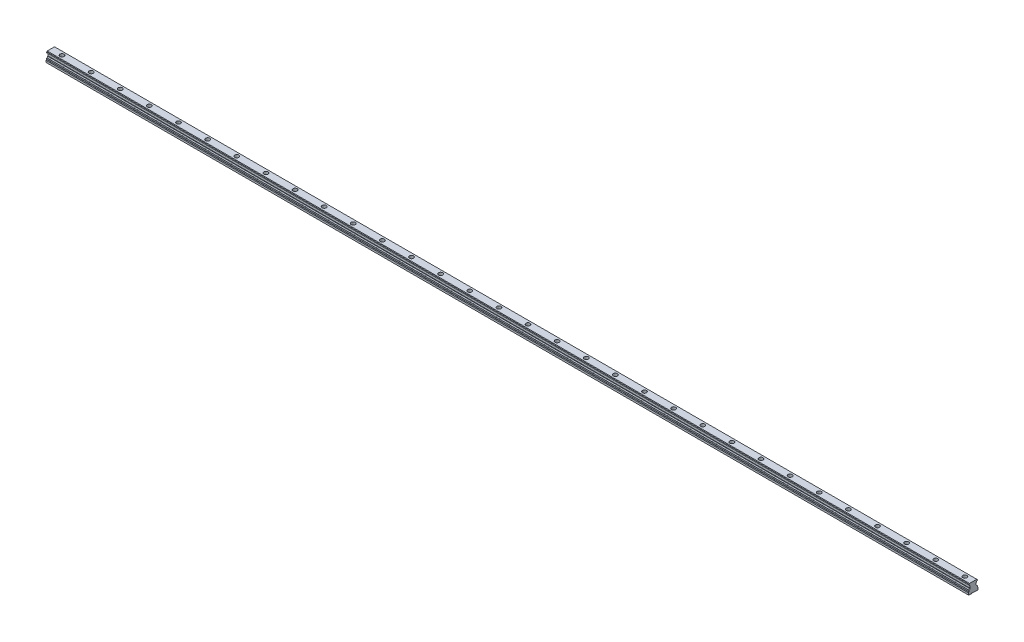
SolidWorks part; units mm, degrees
ref_plane "Front Plane" through (0, 0, 0) normal (0, 0, 1) x (1, 0, 0)
ref_plane "Top Plane" through (0, 0, 0) normal (0, 1, 0) x (1, 0, 0)
ref_plane "Right Plane" through (0, 0, 0) normal (1, 0, 0) x (0, 0, -1)
ref_plane "Plane1" through (58.5, 0, 0) normal (1, 0, 0) x (0, 0, -1)
sketch "Sketch7" plane through (58.5, 0, 0) normal (1, 0, 0) x (0, 0, -1)
  line L30 (-7.709, 8.8831) -> (-8.5, 8.6011)
  line L32 (-8.75, 5.6717) -> (-10, 4.95)
  line L35 (-10, 4.95) -> (-10, 1)
  line L37 (-10, 1) -> (-9, 0)
  line L39 (-4, 0) -> (-3.5, 0.5)
  line L42 (-3.5, 0.5) -> (3.5, 0.5)
  line L48 (3.5, 0.5) -> (4, 0)
  line L52 (4, 0) -> (9, 0)
  line L57 (-8.5, 8.6011) -> (-8.5, 6.1047)
  line L61 (-9, 0) -> (-4, 0)
  line L69 (8.5, 6.1047) -> (8.5, 8.4669)
  line L71 (6.5033, 10.3667) -> (6, 10.87)
  line L72 (6, 10.87) -> (6, 14.93)
  line L73 (6, 14.93) -> (6.5033, 15.4333)
  line L75 (8.5, 17.1989) -> (8.5, 19.3)
  line L77 (7.5, 20.3) -> (-7.5, 20.3)
  line L79 (-8.5, 19.3) -> (-8.5, 17.3331)
  line L81 (-6.5033, 15.4333) -> (-6, 14.93)
  line L82 (-6, 14.93) -> (-6, 10.87)
  line L83 (-6, 10.87) -> (-6.5033, 10.3667)
  line L85 (9, 0) -> (10, 1)
  line L87 (10, 1) -> (10, 4.95)
  line L89 (10, 4.95) -> (8.75, 5.6717)
  line L91 (8.5, 8.4669) -> (8.0847, 8.8822)
  line L93 (7.709, 16.9169) -> (8.5, 17.1989)
  line L95 (8.5, 19.3) -> (7.5, 20.3)
  line L97 (-7.5, 20.3) -> (-8.5, 19.3)
  line L99 (-8.5, 17.3331) -> (-8.0847, 16.9178)
  arc A8 (-8.75, 5.6717) -> (-8.5, 6.1047) centre (-9, 6.1047) ccw
  arc A12 (-7.709, 8.8831) -> (-6.5033, 10.3667) centre (-7.9, 10.27) ccw
  arc A15 (6.5033, 10.3667) -> (8.0847, 8.8822) centre (7.9, 10.27) ccw
  arc A16 (7.709, 16.9169) -> (6.5033, 15.4333) centre (7.9, 15.53) ccw
  arc A17 (-6.5033, 15.4333) -> (-8.0847, 16.9178) centre (-7.9, 15.53) ccw
  arc A19 (8.5, 6.1047) -> (8.75, 5.6717) centre (9, 6.1047) ccw
sketch "Sketch1" [suppressed] plane through (58.5, 0, 0) normal (1, 0, 0) x (0, 0, -1)
  line L0 (-8.5, 0) -> (8.5, 0)
  line L1 (8.5, 0) -> (8.5, 9.0051)
  line L2 (6.5033, 10.3667) -> (6, 10.87)
  line L3 (6, 10.87) -> (6, 14.93)
  line L4 (6, 14.93) -> (6.5033, 15.4333)
  line L5 (8.5, 16.7949) -> (8.5, 20.3)
  line L6 (8.5, 20.3) -> (-8.5, 20.3)
  line L7 (-8.5, 20.3) -> (-8.5, 16.7949)
  line L8 (-6.5033, 15.4333) -> (-6, 14.93)
  line L9 (-6, 14.93) -> (-6, 10.87)
  line L10 (-6, 10.87) -> (-6.5033, 10.3667)
  line L11 (-8.5, 9.0051) -> (-8.5, 0)
  arc A0 (8.5, 9.0051) -> (6.5033, 10.3667) centre (7.9, 10.27) cw
  arc A1 (6.5033, 15.4333) -> (8.5, 16.7949) centre (7.9, 15.53) cw
  arc A2 (-8.5, 16.7949) -> (-6.5033, 15.4333) centre (-7.9, 15.53) cw
  arc A3 (-6.5033, 10.3667) -> (-8.5, 9.0051) centre (-7.9, 10.27) cw
extrude "Boss-Extrude5" add sketch "Sketch7" along normal blind 1900
sketch "Sketch8" plane through (0, 20.3, 0) normal (0, 1, 0) x (1, 0, 0)
  line L0 (2009.9793, 0) -> (1889.6882, 0) construction
  circle A0 centre (1941.4917, 0) radius 4.25
  dimension "D1" = 8.5
extrude "Cut-Extrude1" cut sketch "Sketch8" against normal blind 9
sketch "Sketch9" plane through (0, 11.3, 0) normal (0, 1, 0) x (1, 0, 0)
  circle A0 centre (1941.4917, 0) radius 3
  dimension "D1" = 6
extrude "Cut-Extrude2" cut sketch "Sketch9" against normal through all
pattern_linear "LPattern1" count 35 spacing 60 along (-1, 0, 0) of "Cut-Extrude1", "Cut-Extrude2"
